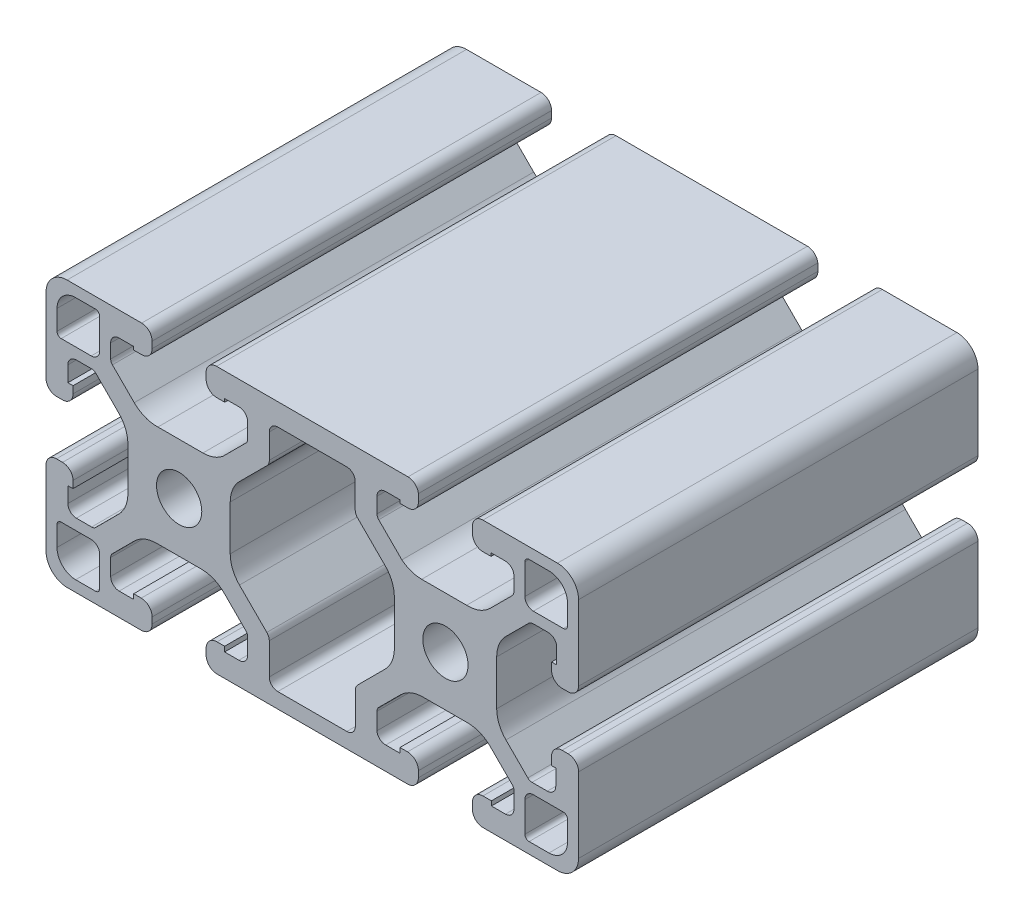
SolidWorks part; units mm, degrees
material "6105-T5 Aluminum"
ref_plane "Front Plane" through (0, 0, 0) normal (0, 0, 1) x (1, 0, 0)
ref_plane "Top Plane" through (0, 0, 0) normal (0, 1, 0) x (1, 0, 0)
ref_plane "Right Plane" through (0, 0, 0) normal (1, 0, 0) x (0, 0, -1)
sketch "Sketch1" plane through (0, 0, 0) normal (0, 0, 1) x (1, 0, 0)
  line L1 (-34.38, 20) -> (-5.62, 20)
  line L2 (-50.0243, -12.1998) -> (-46.7392, -8.9146)
  line L3 (-35.94, 17.51) -> (-35.94, 18.6069)
  line L4 (-30.9397, -6.7352) -> (-26.8324, -10.8426)
  line L5 (-32.3247, 3.3825) -> (-32.3289, -3.3756)
  line L6 (-26.8214, 10.8451) -> (-30.9313, 6.7404)
  line L7 (-26.4494, 15.43) -> (-26.4494, 11.7432)
  line L8 (-20, 16.6968) -> (-25.1787, 16.7)
  line L9 (-34.37, 15.94) -> (-33.1517, 15.94)
  line L10 (-33.1517, 16.4117) -> (-33.1517, 15.94)
  line L11 (-25.1904, -17.7174) -> (-14.8096, -17.7174)
  line L12 (-26.4604, -16.4474) -> (-26.4604, -11.7406)
  line L13 (-33.1517, 16.4117) -> (-31.0437, 16.4117)
  line L14 (-29.715, 12.8476) -> (-29.715, 15.1431)
  line L15 (-33.4586, 8.7397) -> (-29.9761, 12.2179)
  line L16 (-43.1872, 7.7) -> (-36.4245, 7.7)
  line L17 (-57.72, 11.94) -> (-53.21, 11.94)
  line L18 (-51.935, 13.21) -> (-51.935, 17.72)
  line L19 (-55.545, 18.35) -> (-52.565, 18.35)
  line L20 (-58.345, 15.55) -> (-58.345, 12.57)
  line L21 (-46.7456, 9.087) -> (-50.0243, 12.3658)
  line L22 (-50.285, 12.9951) -> (-50.285, 15.0869)
  line L23 (-49.015, 16.3569) -> (-46.8483, 16.3569)
  line L24 (-46.8483, 16.3569) -> (-46.8483, 15.8852)
  line L25 (-46.8483, 15.8852) -> (-45.63, 15.8852)
  line L26 (-44.06, 17.4552) -> (-44.06, 18.43)
  line L27 (-56.83, 20) -> (-45.63, 20)
  line L28 (-51.935, -17.72) -> (-51.935, -13.21)
  line L29 (-60, 16.83) -> (-60, 13)
  line L30 (-60, 5.5719) -> (-60, 13)
  line L31 (-58.4311, 4.06) -> (-57.51, 4.06)
  line L32 (-55.94, 5.63) -> (-55.94, 6.6964)
  line L33 (-56.715, 6.6964) -> (-55.94, 6.6964)
  line L34 (-56.715, 6.6964) -> (-56.715, 9.02)
  line L35 (-55.445, 10.29) -> (-53.1501, 10.29)
  line L36 (-52.5208, 10.0293) -> (-49.0912, 6.5998)
  line L37 (-47.7, 3.241) -> (-47.7, -3.241)
  line L38 (-52.5208, -10.0293) -> (-49.0912, -6.5998)
  line L39 (-55.445, -10.29) -> (-53.1501, -10.29)
  line L40 (-56.715, -9.02) -> (-56.715, -6.6964)
  line L41 (-55.94, -6.6964) -> (-56.715, -6.6964)
  line L42 (-55.94, -6.6964) -> (-55.94, -5.63)
  line L43 (-58.4311, -4.06) -> (-57.51, -4.06)
  line L44 (-60, -16.83) -> (-60, -5.5719)
  line L45 (-57.72, -11.94) -> (-53.21, -11.94)
  line L46 (-56.83, -20) -> (-45.6944, -20)
  line L47 (-34.3056, -20) -> (-26.9396, -20)
  line L48 (-49.015, -16.5584) -> (-46.8283, -16.5584)
  line L49 (-44.06, -17.4474) -> (-44.06, -18.3656)
  line L50 (-46.8283, -15.813) -> (-45.6944, -15.813)
  line L51 (-46.8283, -16.5584) -> (-46.8283, -15.813)
  line L52 (-50.285, -15.2884) -> (-50.285, -12.8291)
  line L53 (5.63, 20) -> (14.2818, 20)
  line L54 (-43.3804, -7.5234) -> (-36.6196, -7.5234)
  line L55 (-33.2608, -8.9146) -> (-29.9757, -12.1998)
  line L56 (-29.715, -12.8291) -> (-29.715, -15.3686)
  line L57 (-33.1717, -16.5584) -> (-31.0293, -16.5584)
  line L58 (-33.1717, -16.5584) -> (-33.1717, -15.813)
  line L59 (-34.3056, -15.813) -> (-33.1717, -15.813)
  line L60 (-35.94, -17.4474) -> (-35.94, -18.3656)
  line L61 (-26.9396, -20) -> (-13.0604, -20)
  line L62 (-13.0604, -20) -> (-5.6944, -20)
  line L63 (-59.8916, 0) -> (0, 0) construction
  line L64 (5.6944, -20) -> (14.3223, -20)
  line L65 (-4.06, -17.4474) -> (-4.06, -18.3656)
  line L66 (-6.8283, -15.813) -> (-5.6944, -15.813)
  line L67 (-6.8283, -16.5584) -> (-6.8283, -15.813)
  line L68 (-8.9707, -16.5584) -> (-6.8283, -16.5584)
  line L69 (-10.285, -12.8291) -> (-10.285, -15.3686)
  line L70 (-10.0243, -12.1998) -> (-6.7392, -8.9146)
  line L71 (3.3834, -7.5234) -> (-3.3804, -7.5234)
  line L72 (10.0243, -12.1998) -> (6.7392, -8.9146)
  line L73 (10.285, -15.2884) -> (10.285, -12.8291)
  line L74 (6.907, -16.5584) -> (9.015, -16.5584)
  line L75 (6.907, -15.8852) -> (6.907, -16.5584)
  line L76 (5.63, -15.8852) -> (6.907, -15.8852)
  line L77 (4.06, -18.4313) -> (4.06, -17.4552)
  line L78 (-13.1786, 10.8451) -> (-9.0687, 6.7404)
  line L79 (16.83, -20) -> (14.3223, -20)
  line L80 (20, -16.83) -> (20, -5.5696)
  line L81 (20, 5.5719) -> (20, 13)
  line L82 (17.51, -3.9996) -> (18.43, -3.9996)
  line L83 (15.94, -6.7799) -> (15.94, -5.5696)
  line L84 (16.5725, -6.7799) -> (15.94, -6.7799)
  line L85 (16.5725, -9.1555) -> (16.5725, -6.7799)
  line L86 (13.0076, -10.4255) -> (15.3025, -10.4255)
  line L87 (9.0891, -6.8716) -> (12.3778, -10.1644)
  line L88 (7.7, 3.241) -> (7.7, -3.515)
  line L89 (12.5208, 10.0293) -> (9.0912, 6.5998)
  line L90 (15.445, 10.29) -> (13.1501, 10.29)
  line L91 (16.715, 6.6964) -> (16.715, 9.02)
  line L92 (15.94, 6.6964) -> (16.715, 6.6964)
  line L93 (15.94, 5.63) -> (15.94, 6.6964)
  line L94 (18.4311, 4.06) -> (17.51, 4.06)
  line L95 (18.345, -15.55) -> (18.345, -12.57)
  line L96 (20, 16.83) -> (20, 13)
  line L97 (14.2818, 20) -> (16.83, 20)
  line L98 (11.935, -17.72) -> (11.935, -13.21)
  line L99 (4.06, 17.4552) -> (4.06, 18.43)
  line L100 (6.8483, 15.8852) -> (5.63, 15.8852)
  line L101 (6.8483, 16.3569) -> (6.8483, 15.8852)
  line L102 (9.015, 16.3569) -> (6.8483, 16.3569)
  line L103 (10.285, 12.9951) -> (10.285, 15.0869)
  line L104 (6.7456, 9.087) -> (10.0243, 12.3658)
  line L105 (18.345, 15.55) -> (18.345, 12.57)
  line L106 (12.565, 18.35) -> (15.545, 18.35)
  line L107 (11.935, 13.21) -> (11.935, 17.72)
  line L108 (17.72, 11.94) -> (13.21, 11.94)
  line L109 (3.1872, 7.7) -> (-3.5688, 7.7)
  line L110 (-6.5414, 8.7397) -> (-10.0239, 12.2179)
  line L111 (-10.285, 12.8476) -> (-10.285, 15.1431)
  line L112 (-8.9563, 16.4117) -> (-6.8483, 16.4117)
  line L113 (-13.5396, -16.4474) -> (-13.5396, -11.7406)
  line L114 (-58.345, -15.55) -> (-58.345, -12.57)
  line L115 (-6.8483, 16.4117) -> (-6.8483, 15.94)
  line L116 (-6.8483, 15.94) -> (-5.63, 15.94)
  line L117 (-20, 16.6968) -> (-14.8206, 16.7)
  line L118 (-13.5506, 15.43) -> (-13.5506, 11.7432)
  line L119 (-55.545, -18.35) -> (-52.565, -18.35)
  line L120 (-7.6753, 3.3825) -> (-7.6711, -3.3756)
  line L121 (-9.0624, -6.7373) -> (-13.1676, -10.8426)
  line L122 (-4.06, 17.51) -> (-4.06, 18.6069)
  line L129 (17.72, -11.94) -> (13.21, -11.94)
  line L131 (12.565, -18.35) -> (15.545, -18.35)
  line L133 (-40, 11.7412) -> (-40, -12.5149) construction
  line L134 (0, 12.6864) -> (0, -12.5149) construction
  line L135 (-40, 0) -> (-67.3415, -27.3415) construction
  arc A0 (-35.94, 18.6069) -> (-34.38, 20) centre (-34.38, 18.43) cw
  circle A1 centre (-40, 0) radius 3.4
  arc A2 (-34.37, 15.94) -> (-35.94, 17.51) centre (-34.37, 17.51) cw
  arc A3 (-31.0437, 16.4117) -> (-29.715, 15.1431) centre (-30.985, 15.1431) cw
  arc A4 (-33.4586, 8.7397) -> (-36.4245, 7.7) centre (-36.4245, 12.45) cw
  arc A5 (-43.1872, 7.7) -> (-46.7456, 9.087) centre (-43.3868, 12.4458) cw
  arc A6 (-32.3289, -3.3756) -> (-30.9397, -6.7352) centre (-27.5789, -3.3786) ccw
  arc A7 (-30.9313, 6.7404) -> (-32.3247, 3.3825) centre (-27.5747, 3.3795) ccw
  arc A8 (-26.8214, 10.8451) -> (-26.4494, 11.7432) centre (-27.7194, 11.7432) ccw
  arc A9 (-25.1787, 16.7) -> (-26.4494, 15.43) centre (-25.1794, 15.43) ccw
  arc A10 (-29.715, 12.8476) -> (-29.9761, 12.2179) centre (-30.605, 12.8476) cw
  arc A11 (-26.4604, -16.4474) -> (-25.1904, -17.7174) centre (-25.1904, -16.4474) ccw
  arc A12 (-26.4604, -11.7406) -> (-26.8324, -10.8426) centre (-27.7304, -11.7406) ccw
  arc A13 (-53.21, 11.94) -> (-51.935, 13.21) centre (-53.205, 13.21) ccw
  arc A14 (-51.935, 17.72) -> (-52.565, 18.35) centre (-52.565, 17.72) ccw
  arc A15 (-55.545, 18.35) -> (-58.345, 15.55) centre (-55.545, 15.55) ccw
  arc A16 (-58.345, 12.57) -> (-57.72, 11.94) centre (-57.715, 12.57) ccw
  arc A17 (-50.285, 12.9951) -> (-50.0243, 12.3658) centre (-49.395, 12.9951) ccw
  arc A18 (-49.015, 16.3569) -> (-50.285, 15.0869) centre (-49.015, 15.0869) ccw
  arc A19 (-45.63, 15.8852) -> (-44.06, 17.4552) centre (-45.63, 17.4552) ccw
  arc A20 (-44.06, 18.43) -> (-45.63, 20) centre (-45.63, 18.43) ccw
  arc A21 (-56.83, 20) -> (-60, 16.83) centre (-56.83, 16.83) ccw
  arc A22 (-60, 5.5719) -> (-58.4311, 4.06) centre (-58.4311, 5.63) ccw
  arc A23 (-57.51, 4.06) -> (-55.94, 5.63) centre (-57.51, 5.63) ccw
  arc A24 (-55.445, 10.29) -> (-56.715, 9.02) centre (-55.445, 9.02) ccw
  arc A25 (-52.5208, 10.0293) -> (-53.1501, 10.29) centre (-53.1501, 9.4) ccw
  arc A26 (-47.7, 3.241) -> (-49.0912, 6.5998) centre (-52.45, 3.241) ccw
  arc A27 (-47.7, -3.241) -> (-49.0912, -6.5998) centre (-52.45, -3.241) cw
  arc A28 (-52.5208, -10.0293) -> (-53.1501, -10.29) centre (-53.1501, -9.4) cw
  arc A29 (-55.445, -10.29) -> (-56.715, -9.02) centre (-55.445, -9.02) cw
  arc A30 (-57.51, -4.06) -> (-55.94, -5.63) centre (-57.51, -5.63) cw
  arc A31 (-60, -5.5719) -> (-58.4311, -4.06) centre (-58.4311, -5.63) cw
  arc A32 (-60, -16.83) -> (-56.83, -20) centre (-56.83, -16.83) ccw
  arc A33 (-44.06, -18.3656) -> (-45.6944, -20) centre (-45.6944, -18.3656) cw
  arc A34 (-45.6944, -15.813) -> (-44.06, -17.4474) centre (-45.6944, -17.4474) cw
  arc A35 (-50.285, -15.2884) -> (-49.015, -16.5584) centre (-49.015, -15.2884) ccw
  arc A36 (-50.0243, -12.1998) -> (-50.285, -12.8291) centre (-49.395, -12.8291) ccw
  arc A37 (-43.3804, -7.5234) -> (-46.7392, -8.9146) centre (-43.3804, -12.2734) ccw
  arc A38 (-33.2608, -8.9146) -> (-36.6196, -7.5234) centre (-36.6196, -12.2734) ccw
  arc A39 (-29.715, -12.8291) -> (-29.9757, -12.1998) centre (-30.605, -12.8291) ccw
  arc A40 (-31.0293, -16.5584) -> (-29.715, -15.3686) centre (-30.9825, -15.2892) ccw
  arc A41 (-34.3056, -15.813) -> (-35.94, -17.4474) centre (-34.3056, -17.4474) ccw
  arc A42 (-35.94, -18.3656) -> (-34.3056, -20) centre (-34.3056, -18.3656) ccw
  arc A43 (-4.06, -18.3656) -> (-5.6944, -20) centre (-5.6944, -18.3656) cw
  arc A44 (-5.6944, -15.813) -> (-4.06, -17.4474) centre (-5.6944, -17.4474) cw
  arc A45 (-8.9707, -16.5584) -> (-10.285, -15.3686) centre (-9.0175, -15.2892) cw
  arc A46 (-10.285, -12.8291) -> (-10.0243, -12.1998) centre (-9.395, -12.8291) cw
  arc A47 (-6.7392, -8.9146) -> (-3.3804, -7.5234) centre (-3.3804, -12.2734) cw
  arc A48 (3.3834, -7.5234) -> (6.7392, -8.9146) centre (3.3804, -12.2734) cw
  arc A49 (10.0243, -12.1998) -> (10.285, -12.8291) centre (9.395, -12.8291) cw
  arc A50 (10.285, -15.2884) -> (9.015, -16.5584) centre (9.015, -15.2884) cw
  arc A51 (4.06, -17.4552) -> (5.63, -15.8852) centre (5.63, -17.4552) cw
  arc A52 (5.6944, -20) -> (4.06, -18.4313) centre (5.63, -18.4313) cw
  arc A53 (20, -16.83) -> (16.83, -20) centre (16.83, -16.83) cw
  arc A54 (18.43, -3.9996) -> (20, -5.5696) centre (18.43, -5.5696) cw
  arc A55 (15.94, -5.5696) -> (17.51, -3.9996) centre (17.51, -5.5696) cw
  arc A56 (16.5725, -9.1555) -> (15.3025, -10.4255) centre (15.3025, -9.1555) cw
  arc A57 (13.0076, -10.4255) -> (12.3778, -10.1644) centre (13.0076, -9.5355) cw
  arc A58 (9.0891, -6.8716) -> (7.7, -3.515) centre (12.45, -3.515) cw
  arc A59 (7.7, 3.241) -> (9.0912, 6.5998) centre (12.45, 3.241) cw
  arc A60 (12.5208, 10.0293) -> (13.1501, 10.29) centre (13.1501, 9.4) cw
  arc A61 (15.445, 10.29) -> (16.715, 9.02) centre (15.445, 9.02) cw
  arc A62 (17.51, 4.06) -> (15.94, 5.63) centre (17.51, 5.63) cw
  arc A63 (20, 5.5719) -> (18.4311, 4.06) centre (18.4311, 5.63) cw
  arc A64 (16.83, 20) -> (20, 16.83) centre (16.83, 16.83) cw
  arc A65 (4.06, 18.43) -> (5.63, 20) centre (5.63, 18.43) cw
  arc A66 (5.63, 15.8852) -> (4.06, 17.4552) centre (5.63, 17.4552) cw
  arc A67 (9.015, 16.3569) -> (10.285, 15.0869) centre (9.015, 15.0869) cw
  arc A68 (10.285, 12.9951) -> (10.0243, 12.3658) centre (9.395, 12.9951) cw
  arc A69 (18.345, 12.57) -> (17.72, 11.94) centre (17.715, 12.57) cw
  arc A70 (15.545, 18.35) -> (18.345, 15.55) centre (15.545, 15.55) cw
  arc A71 (11.935, 17.72) -> (12.565, 18.35) centre (12.565, 17.72) cw
  arc A72 (13.21, 11.94) -> (11.935, 13.21) centre (13.205, 13.21) cw
  arc A73 (-13.5396, -11.7406) -> (-13.1676, -10.8426) centre (-12.2696, -11.7406) cw
  arc A74 (-13.5396, -16.4474) -> (-14.8096, -17.7174) centre (-14.8096, -16.4474) cw
  arc A75 (-10.285, 12.8476) -> (-10.0239, 12.2179) centre (-9.395, 12.8476) ccw
  arc A76 (-14.8206, 16.7) -> (-13.5506, 15.43) centre (-14.8206, 15.43) cw
  arc A77 (-13.1786, 10.8451) -> (-13.5506, 11.7432) centre (-12.2806, 11.7432) cw
  arc A78 (-9.0687, 6.7404) -> (-7.6753, 3.3825) centre (-12.4253, 3.3795) cw
  arc A79 (-7.6711, -3.3756) -> (-9.0624, -6.7373) centre (-12.4211, -3.3786) cw
  arc A80 (3.1872, 7.7) -> (6.7456, 9.087) centre (3.3868, 12.4458) ccw
  arc A81 (-6.5414, 8.7397) -> (-3.5688, 7.7) centre (-3.5755, 12.45) ccw
  arc A82 (-8.9563, 16.4117) -> (-10.285, 15.1431) centre (-9.015, 15.1431) ccw
  arc A83 (-5.63, 15.94) -> (-4.06, 17.51) centre (-5.63, 17.51) ccw
  circle A84 centre (0, 0) radius 3.4
  arc A85 (-4.06, 18.6069) -> (-5.62, 20) centre (-5.62, 18.43) ccw
  arc A86 (-58.345, -12.57) -> (-57.72, -11.94) centre (-57.715, -12.57) cw
  arc A87 (-55.545, -18.35) -> (-58.345, -15.55) centre (-55.545, -15.55) cw
  arc A88 (-51.935, -17.72) -> (-52.565, -18.35) centre (-52.565, -17.72) cw
  arc A89 (-53.21, -11.94) -> (-51.935, -13.21) centre (-53.205, -13.21) cw
  arc A90 (13.21, -11.94) -> (11.935, -13.21) centre (13.205, -13.21) ccw
  arc A91 (11.935, -17.72) -> (12.565, -18.35) centre (12.565, -17.72) ccw
  arc A92 (15.545, -18.35) -> (18.345, -15.55) centre (15.545, -15.55) ccw
  arc A93 (18.345, -12.57) -> (17.72, -11.94) centre (17.715, -12.57) ccw
  dimension "D2" = 6.8
  dimension "D1" = 40
  dimension "D3" = 40
  dimension "D4" = 8.12
  dimension "D5" = 80
  dimension "D6" = 3.3
  dimension "D7" = 12.3
  dimension "D8" = 45
  dimension "D9" = 20.57
  dimension "D10" = 4.06
  dimension "D15" = 1.5145
  dimension "D16" = 1.65
extrude "Extrude1" add sketch "Sketch1" against normal blind 60
